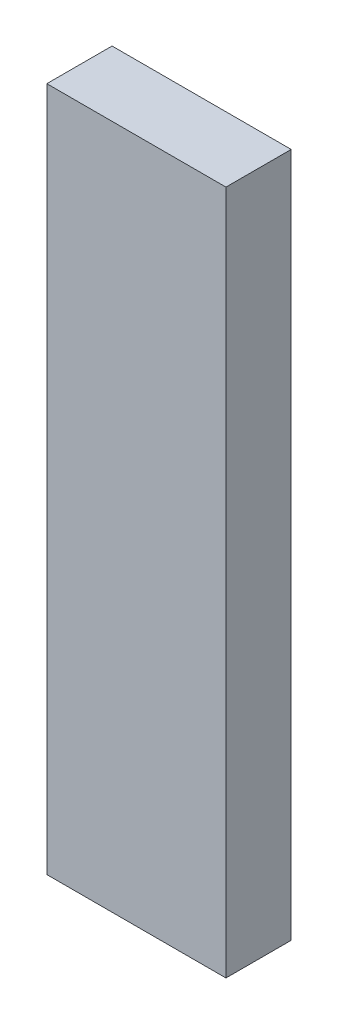
SolidWorks part; units mm, degrees
ref_plane "Front Plane" through (0, 0, 0) normal (0, 0, 1) x (1, 0, 0)
ref_plane "Top Plane" through (0, 0, 0) normal (0, 1, 0) x (1, 0, 0)
ref_plane "Right Plane" through (0, 0, 0) normal (1, 0, 0) x (0, 0, -1)
sketch "Sketch1" plane through (0, 0, 0) normal (0, 1, 0) x (1, 0, 0)
  line L1 (-8.6487, -3.1496) -> (8.6487, -3.1496)
  line L2 (-8.6487, -3.1496) -> (-8.6487, 3.1496)
  line L3 (-8.6487, 3.1496) -> (8.6487, 3.1496)
  line L4 (8.6487, -3.1496) -> (8.6487, 3.1496)
  line L5 (-8.6487, -3.1496) -> (8.6487, 3.1496) construction
  line L6 (-8.6487, 3.1496) -> (8.6487, -3.1496) construction
  point P0 (0, 0)
  dimension "D1" = 6.2992
  dimension "D2" = 17.2974
extrude "Boss-Extrude1" add sketch "Sketch1" along normal blind 66.1416
